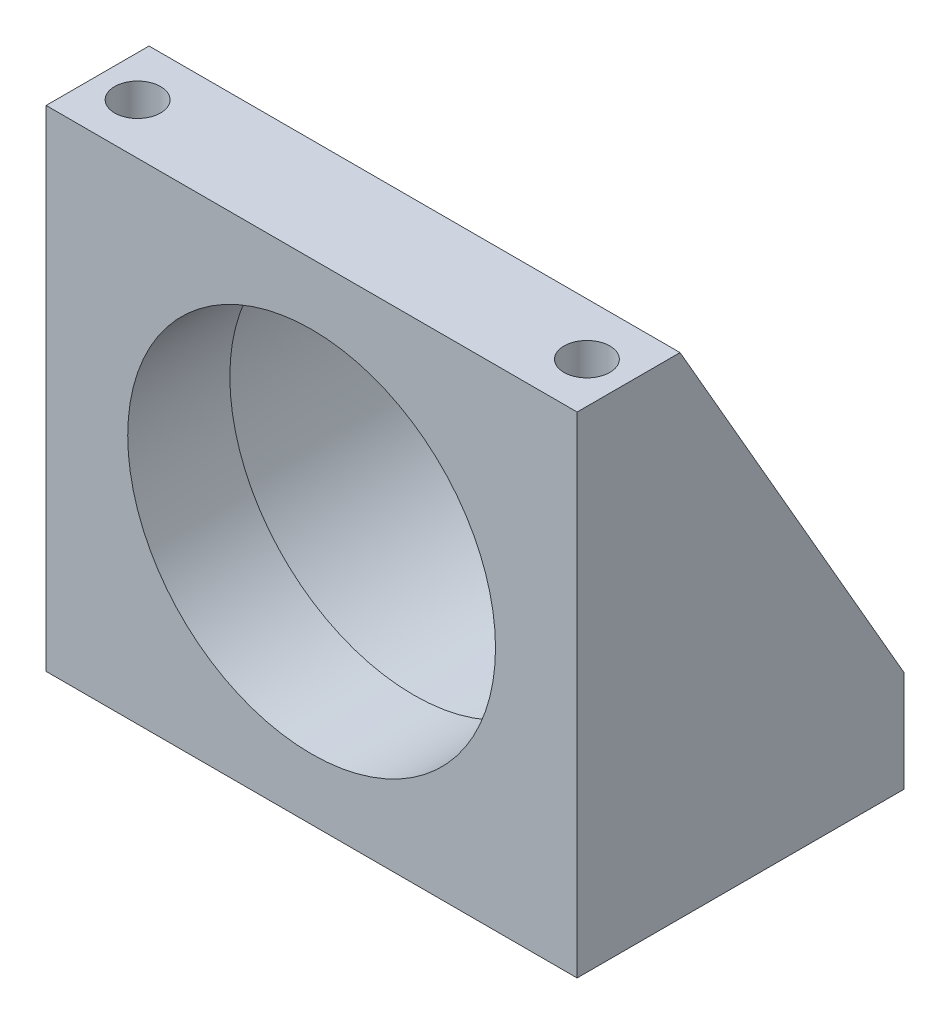
SolidWorks part; units mm, degrees
material "Alloy Steel"
ref_plane "Front Plane" through (0, 0, 0) normal (0, 0, 1) x (1, 0, 0)
ref_plane "Top Plane" through (0, 0, 0) normal (0, 1, 0) x (1, 0, 0)
ref_plane "Right Plane" through (0, 0, 0) normal (1, 0, 0) x (0, 0, -1)
sketch "Sketch1" plane through (0, 0, 0) normal (0, 0, 1) x (1, 0, 0)
  line L1 (-41.275, 76.2) -> (41.275, 76.2)
  line L2 (-41.275, 76.2) -> (-41.275, 0)
  line L3 (-41.275, 0) -> (41.275, 0)
  line L4 (41.275, 76.2) -> (41.275, 0)
  circle A0 centre (0, 38.1) radius 28.5877
  dimension "D4" = 57.1754
  dimension "D1" = 82.55
  dimension "D2" = 76.2
  dimension "D3" = 38.1
extrude "Extrude1" add sketch "Sketch1" against normal blind 50.8
sketch "Sketch2" plane through (41.275, 0, 0) normal (1, 0, 0) x (0, 0, -1)
  line L0 (16.002, 76.2) -> (50.8, 15.748)
  line L1 (0, 0) -> (0, 76.2) construction
  line L2 (50.8, 0) -> (0, 0) construction
  line L4 (0, 76.2) -> (0, 0)
  line L5 (0, 0) -> (50.8, 0)
  line L6 (50.8, 0) -> (50.8, 76.2)
  line L7 (50.8, 76.2) -> (0, 76.2)
  line L10 (50.8, 15.748) -> (50.8, 76.2)
  line L11 (50.8, 76.2) -> (16.002, 76.2)
  dimension "D2" = 16.002
  dimension "D3" = 15.748
  dimension "D1" = 0
extrude "Cut-Extrude1" cut sketch "Sketch2" against normal through all
sketch "Sketch3" plane through (0, 0, -50.8) normal (0, 0, -1) x (-1, 0, 0)
  circle A0 centre (0, 38.1) radius 30.988
  dimension "D1" = 61.976
extrude "Cut-Extrude2" cut sketch "Sketch3" against normal offset from surface (34.925 mm away) 15.875 up to face at (28.5877, 38.1, 0)
fillet "Fillet1" radius 1.524 1 edges at (30.988, 38.1, -15.875)
hole_wizard "Hole1" positions "Sketch5" profile "Sketch4" legacy end condition up to next
sketch "Sketch5" plane through (0, 76.2, 0) normal (0, 1, 0) x (-1, 0, 0)
  line L0 (-41.275, -16.002) -> (-41.275, 0) construction
  line L1 (-41.275, 0) -> (41.275, 0) construction
  point P0 (34.925, -7.874)
  point P1 (-34.925, -7.874)
  dimension "D1" = 6.35
  dimension "D2" = 7.874
  dimension "D3" = 69.85
sketch "Sketch4" plane through (-34.925, 76.2, -7.874) normal (1, 0, 0) x (0, 0, 1)
  line L0 (0, 0) -> (0, 76.2)
  line L1 (0, 76.2) -> (3.5687, 76.2)
  line L2 (3.5687, 76.2) -> (3.5687, 0)
  line L3 (3.5687, 0) -> (0, 0)
  line L4 (0, 110) -> (0, -10) construction
  dimension "Diameter" = 7.1374
  dimension "Depth" = 76.2
